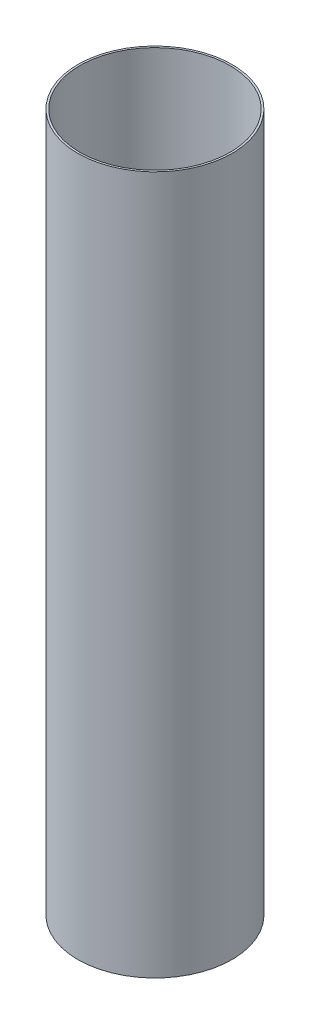
SolidWorks part; units mm, degrees
ref_plane "Front Plane" through (0, 0, 0) normal (0, 0, 1) x (1, 0, 0)
ref_plane "Top Plane" through (0, 0, 0) normal (0, 1, 0) x (1, 0, 0)
ref_plane "Right Plane" through (0, 0, 0) normal (1, 0, 0) x (0, 0, -1)
sketch "Sketch1" plane through (0, 0, 0) normal (0, 1, 0) x (1, 0, 0)
  circle A0 centre (0, 0) radius 98.425
  circle A1 centre (0, 0) radius 100.965
  dimension "D1" = 2.54
  dimension "D2" = 196.85
extrude "Boss-Extrude1" add sketch "Sketch1" along normal blind 914.4
